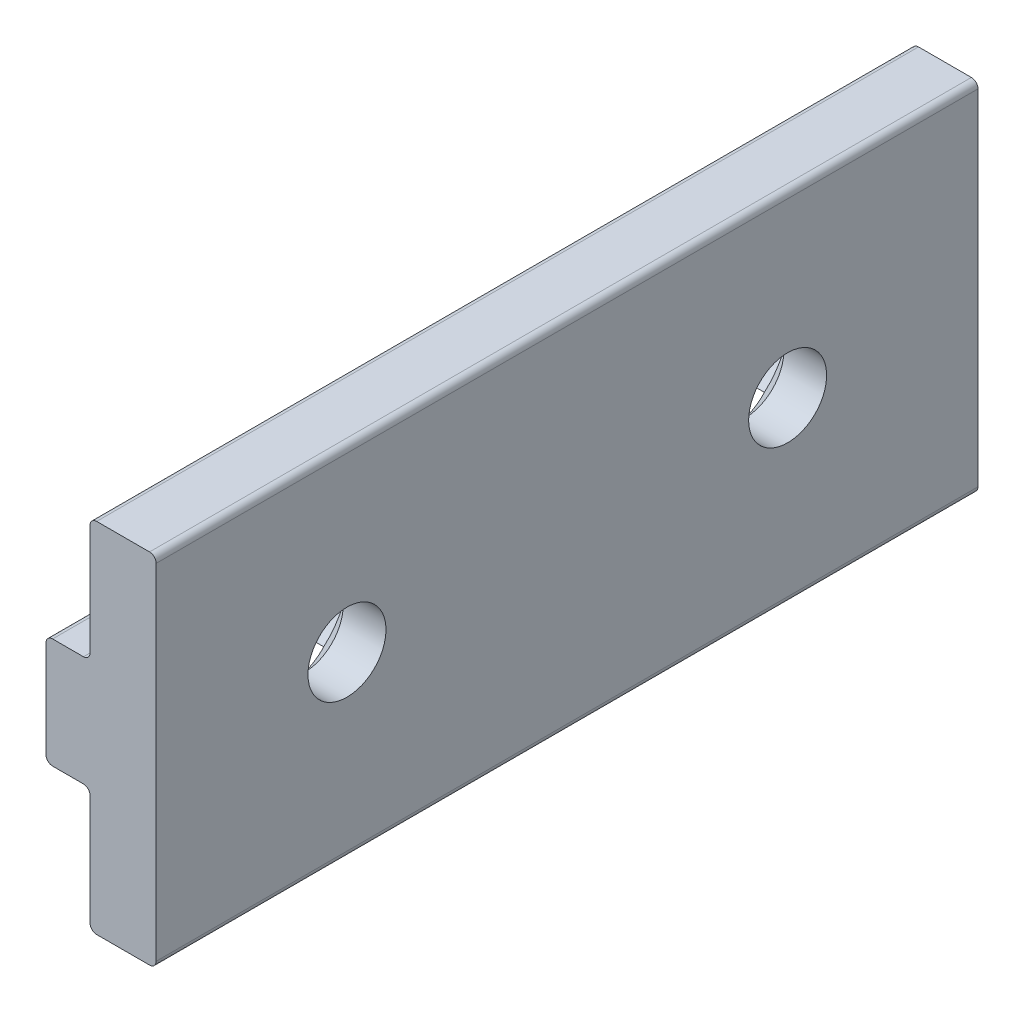
SolidWorks part; units mm, degrees
material "PE High Density"
ref_plane "Front Plane" through (0, 0, 0) normal (0, 0, 1) x (1, 0, 0)
ref_plane "Top Plane" through (0, 0, 0) normal (0, 1, 0) x (1, 0, 0)
ref_plane "Right Plane" through (0, 0, 0) normal (1, 0, 0) x (0, 0, -1)
sketch "Sketch1" plane through (0, 0, 0) normal (0, 0, 1) x (1, 0, 0)
  line L0 (761.5282, 570.2297) -> (761.5282, 550.3669)
  line L1 (757.7182, 550.3669) -> (757.7182, 556.7423)
  line L2 (757.7182, 570.2297) -> (757.7182, 563.8543)
  line L3 (761.1472, 570.6107) -> (758.0992, 570.6107)
  line L4 (755.1782, 563.0923) -> (755.1782, 557.5043)
  line L5 (757.3372, 563.4733) -> (755.5592, 563.4733)
  line L6 (757.3372, 557.1233) -> (755.5592, 557.1233)
  line L7 (761.1472, 549.9859) -> (758.0992, 549.9859)
  arc A0 (758.0992, 570.6107) -> (757.7182, 570.2297) centre (758.0992, 570.2297) ccw
  arc A1 (761.5282, 570.2297) -> (761.1472, 570.6107) centre (761.1472, 570.2297) ccw
  arc A2 (755.5592, 563.4733) -> (755.1782, 563.0923) centre (755.5592, 563.0923) ccw
  arc A3 (757.3372, 563.4733) -> (757.7182, 563.8543) centre (757.3372, 563.8543) ccw
  arc A4 (757.7182, 556.7423) -> (757.3372, 557.1233) centre (757.3372, 556.7423) ccw
  arc A5 (755.1782, 557.5043) -> (755.5592, 557.1233) centre (755.5592, 557.5043) ccw
  arc A6 (761.1472, 549.9859) -> (761.5282, 550.3669) centre (761.1472, 550.3669) ccw
  arc A7 (757.7182, 550.3669) -> (758.0992, 549.9859) centre (758.0992, 550.3669) ccw
  point P24 (757.8471, 570.5154)
extrude "Extrude1" add sketch "Sketch1" along normal blind 47.371
sketch "Sketch2" plane through (755.1782, 0, 0) normal (-1, 0, 0) x (0, 0, 1)
  circle A0 centre (10.9728, 560.2983) radius 1.3843
  circle A1 centre (36.3728, 560.2983) radius 1.3843
extrude "Cut-Extrude1" cut sketch "Sketch2" against normal through all
hole_wizard "CSK for #8 Flat Head Machine Screw (100)1" positions "3DSketch1" profile "Sketch3" countersink size "#8" standard "Ansi Inch" end condition through all
sketch3d "3DSketch1"
  line L0 (761.5282, 560.2983, 10.9728) -> (755.1782, 560.2983, 10.9728) construction
  line L1 (761.5282, 560.2983, 36.3728) -> (755.1782, 560.2983, 36.3728) construction
  point P0 (755.1782, 560.2983, 10.9728)
  point P2 (755.1782, 560.2983, 36.3728)
sketch "Sketch3" plane through (755.1782, 560.2983, 10.9728) normal (0, 1, 0) x (0, 0, 1)
  line L0 (0, 0) -> (0, 6.35)
  line L1 (0, 6.35) -> (2.2479, 6.35)
  line L2 (2.2479, 6.35) -> (2.2479, 3.887)
  line L3 (2.2479, 3.887) -> (4.2164, 2.2352)
  line L4 (4.2164, 2.2352) -> (4.2164, 0)
  line L6 (4.2164, 0) -> (0, 0)
  line L7 (-2.2479, 3.887) -> (-4.2164, 2.2352) construction
  line L11 (0, -6.35) -> (0, 107.95) construction
  dimension "Thru Hole Dia." = 4.4958
  dimension "Thru Hole Depth" = 6.35
  dimension "C'Sink Dia." = 8.4328
  dimension "C'Sink Angle" = 100
  dimension "Head Clearance" = 2.2352
